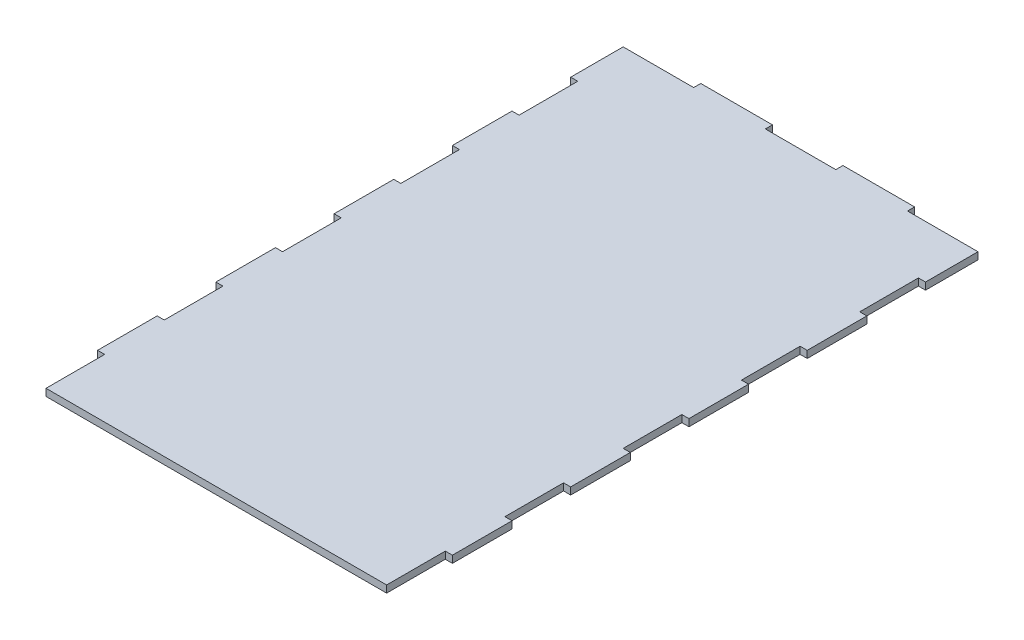
SolidWorks part; units mm, degrees
ref_plane "Front Plane" through (0, 0, 0) normal (0, 0, 1) x (1, 0, 0)
ref_plane "Top Plane" through (0, 0, 0) normal (0, 1, 0) x (1, 0, 0)
ref_plane "Right Plane" through (0, 0, 0) normal (1, 0, 0) x (0, 0, -1)
sketch "Sketch1" plane through (0, 0, 0) normal (0, 1, 0) x (1, 0, 0)
  line L1 (0, 0) -> (150, 0)
  line L2 (0, 0) -> (0, 250)
  line L3 (0, 250) -> (150, 250)
  line L4 (150, 0) -> (150, 250)
  line L5 (0, 247) -> (29.8, 247)
  line L8 (29.8, 247) -> (29.8, 250)
  line L10 (60.1, 250) -> (60.1, 247)
  line L11 (60.1, 247) -> (89.9, 247)
  line L12 (89.9, 250) -> (89.9, 247)
  line L13 (150, 247) -> (120.2, 247)
  line L16 (120.2, 247) -> (120.2, 250)
  line L17 (150, 224.8) -> (147, 224.8)
  line L19 (150, 200) -> (147, 200)
  line L20 (147, 224.8) -> (147, 200)
  line L21 (150, 174.8) -> (147, 174.8)
  line L22 (147, 174.8) -> (147, 150)
  line L23 (150, 150) -> (147, 150)
  line L25 (150, 124.8) -> (147, 124.8)
  line L26 (147, 124.8) -> (147, 100)
  line L27 (150, 100) -> (147, 100)
  line L29 (150, 74.8) -> (147, 74.8)
  line L30 (147, 74.8) -> (147, 50)
  line L31 (150, 50) -> (147, 50)
  line L33 (150, 24.8) -> (147, 24.8)
  line L34 (147, 24.8) -> (147, 0)
  line L36 (75, -750) -> (75, 49250) construction
  line L37 (0, 24.8) -> (3, 24.8)
  line L38 (3, 24.8) -> (3, 0)
  line L41 (0, 74.8) -> (3, 74.8)
  line L42 (3, 74.8) -> (3, 50)
  line L43 (0, 50) -> (3, 50)
  line L45 (0, 124.8) -> (3, 124.8)
  line L46 (3, 124.8) -> (3, 100)
  line L47 (0, 100) -> (3, 100)
  line L49 (0, 174.8) -> (3, 174.8)
  line L50 (3, 174.8) -> (3, 150)
  line L51 (0, 150) -> (3, 150)
  line L53 (0, 200) -> (3, 200)
  line L54 (3, 224.8) -> (3, 200)
  line L55 (0, 224.8) -> (3, 224.8)
  line L61 (150, 0) -> (147, 0) [skipped]
  point P38 (75, 250)
  dimension "D1" = 250
  dimension "D2" = 150
  dimension "D3" = 3
  dimension "D4" = 3
  dimension "D5" = 3
  dimension "D6" = 29.8
  dimension "D7" = 30.3
  dimension "D8" = 30.3
  dimension "D9" = 29.8
  dimension "D10" = 25.2
  dimension "D11" = 24.8
  dimension "D12" = 3
  dimension "D13" = 5
extrude "Boss-Extrude1" add sketch "Sketch1" along normal blind 3 contours L36 L1 L34 L33 L4 L31 L30 L29 L27 L26 L25 L23 L22 L21 L19 L20 L17 L13 L16 L3 L12 L11 | L1 L36 L11 L10 L3 L8 L5 L2 L55 L54 L53 L49 L50 L51 L45 L46 L47 L41 L42 L43 L37 L38
